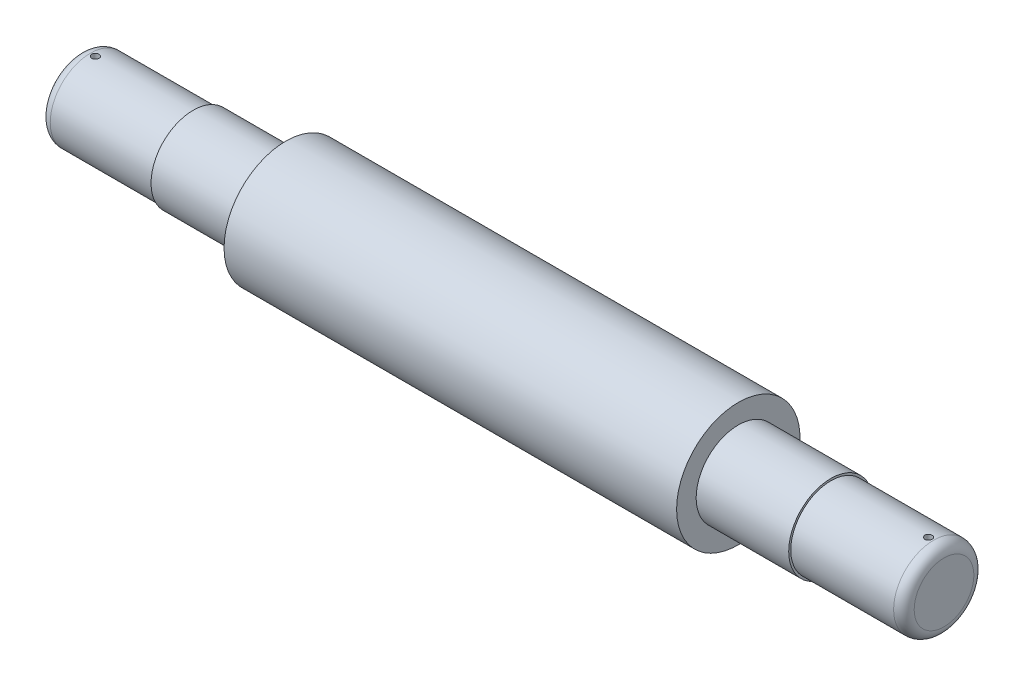
SolidWorks part; units mm, degrees
ref_plane "Ön Düzlem" through (0, 0, 0) normal (0, 0, 1) x (1, 0, 0)
ref_plane "Üst Düzlem" through (0, 0, 0) normal (0, 1, 0) x (1, 0, 0)
ref_plane "Sağ Düzlem" through (0, 0, 0) normal (1, 0, 0) x (0, 0, -1)
sketch "Çizim1" plane through (0, 0, 0) normal (0, 0, 1) x (1, 0, 0)
  line L0 (158.5551, 64.4885) -> (158.5551, 62.4885)
  line L1 (468.5551, 83.4885) -> (468.5551, -36.5115) construction
  line L2 (48.5551, 23.4885) -> (888.5551, 23.4885)
  line L3 (48.5551, 23.4885) -> (48.5551, 62.4885)
  line L4 (48.5551, 62.4885) -> (158.5551, 62.4885)
  line L6 (48.5551, 23.4885) -> (888.5551, 23.4885) construction
  line L7 (158.5551, 64.4885) -> (248.5551, 64.4885)
  line L8 (248.5551, 64.4885) -> (248.5551, 83.4885)
  line L11 (248.5551, 83.4885) -> (688.5551, 83.4885)
  line L13 (778.5551, 64.4885) -> (688.5551, 64.4885)
  line L16 (888.5551, 62.4885) -> (778.5551, 62.4885)
  line L17 (888.5551, 23.4885) -> (888.5551, 62.4885)
  line L19 (778.5551, 64.4885) -> (778.5551, 62.4885)
  line L20 (688.5551, 64.4885) -> (688.5551, 83.4885)
revolve "Döndür1" add sketch "Çizim1" angle 360 about L2
fillet "Radyus1" radius 10 1 edges at (48.5551, 23.4885, 39)
sketch "Çizim2" plane through (48.5551, 0, 0) normal (-1, 0, 0) x (0, 0, 1)
  circle A0 centre (0, 23.4885) radius 3.75
  dimension "D1" = 7.5
extrude "Kes-Ekstrüzyon1" cut sketch "Çizim2" against normal blind 10
fillet "Radyus2" radius 10 1 edges at (888.5551, 23.4885, 39)
ref_plane "Düzlem1" through (0, 63, 0) normal (0, 1, 0) x (1, 0, 0)
sketch "Çizim3" plane through (0, 63, 0) normal (0, 1, 0) x (1, 0, 0)
  line L0 (58.5551, 39) -> (58.5551, -39) construction
  line L1 (58.5551, -39) -> (158.5551, -39) construction
  line L3 (468.5551, -181.6859) -> (468.5551, 60) construction
  line L4 (248.5551, -181.6859) -> (688.5551, -181.6859) construction
  line L5 (688.5551, 60) -> (248.5551, 60) construction
  circle A0 centre (63.5551, 0) radius 3.5
  circle A1 centre (873.5551, 0) radius 3.5
  dimension "D1" = 7
  dimension "D2" = 5
  dimension "D3" = 39
extrude "Kes-Ekstrüzyon2" cut sketch "Çizim3" against normal through all
